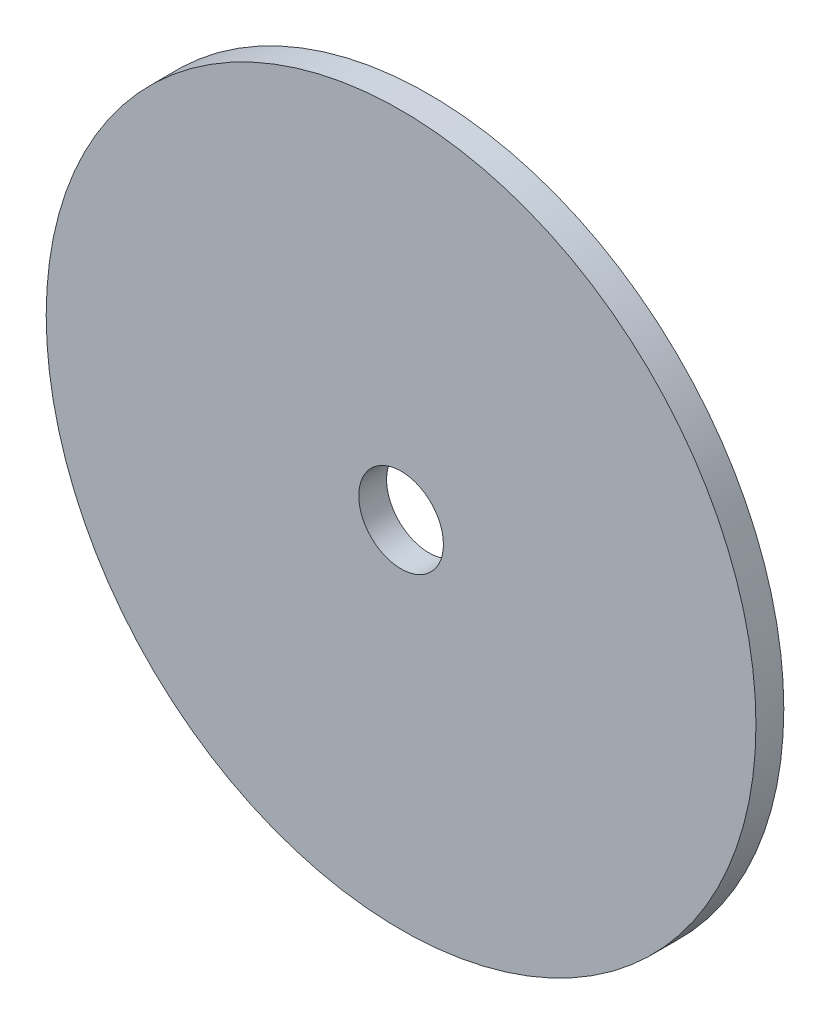
SolidWorks part; units mm, degrees
ref_plane "Front Plane" through (0, 0, 0) normal (0, 0, 1) x (1, 0, 0)
ref_plane "Top Plane" through (0, 0, 0) normal (0, 1, 0) x (1, 0, 0)
ref_plane "Right Plane" through (0, 0, 0) normal (1, 0, 0) x (0, 0, -1)
sketch "Sketch1" plane through (0, 0, 0) normal (0, 0, 1) x (1, 0, 0)
  circle A0 centre (0, 0) radius 63.7004
  circle A5 centre (0, 0) radius 7.6
  point P13 (0, 0)
extrude "Boss-Extrude1" add sketch "Sketch1" along normal blind 5
